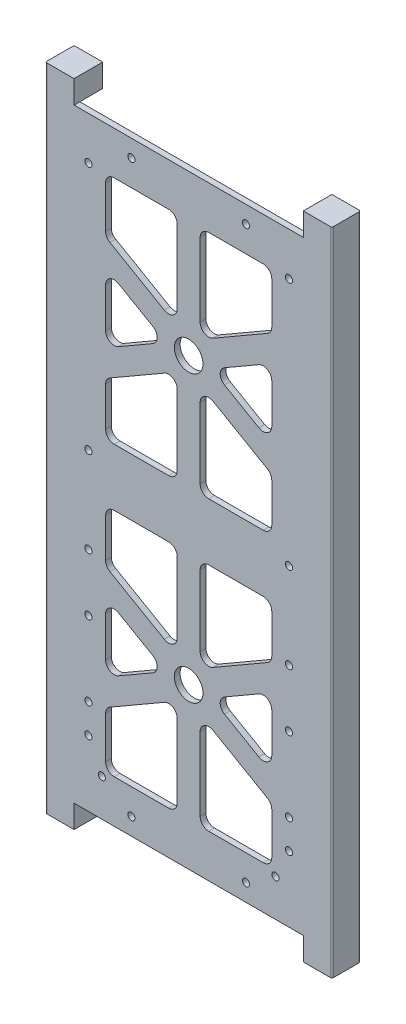
SolidWorks part; units mm, degrees
material "6061-T6 (SS)"
ref_plane "Front Plane" through (0, 0, 0) normal (0, 0, 1) x (1, 0, 0)
ref_plane "Top Plane" through (0, 0, 0) normal (0, 1, 0) x (1, 0, 0)
ref_plane "Right Plane" through (0, 0, 0) normal (1, 0, 0) x (0, 0, -1)
sketch "Sketch1" plane through (0, 0, 0) normal (0, 0, 1) x (1, 0, 0)
  line L1 (0, 0) -> (88, 0)
  line L2 (0, 0) -> (0, 211)
  line L3 (0, 211) -> (88, 211)
  line L4 (88, 0) -> (88, 211)
  dimension "D1" = 88
  dimension "D2" = 211
extrude "Boss-Extrude1" add sketch "Sketch1" along normal blind 2
sketch "Sketch2" plane through (0, 0, 2) normal (0, 0, 1) x (1, 0, 0)
  line L0 (0, 105.5) -> (88, 105.5) construction
  line L1 (0, 211) -> (0, 0) construction
  line L2 (88, 0) -> (88, 211) construction
  line L3 (44, 211) -> (44, 0) construction
  line L4 (88, 211) -> (0, 211) construction
  line L5 (0, 0) -> (88, 0) construction
  line L6 (0, 155.25) -> (88, 155.25) construction
  line L7 (0, 55.75) -> (88, 55.75) construction
  dimension "D1" = 55.75
  dimension "D2" = 55.75
sketch "Sketch3" plane through (0, 0, 2) normal (0, 0, 1) x (1, 0, 0)
  line L0 (0, 155.25) -> (88, 155.25) construction
  line L2 (0, 211) -> (0, 0) construction
  line L3 (15, 196) -> (73, 196)
  line L4 (15, 196) -> (15, 115.5)
  line L5 (15, 115.5) -> (73, 115.5)
  line L6 (73, 196) -> (73, 115.5)
  line L7 (88, 211) -> (0, 211) construction
  line L8 (88, 0) -> (88, 211) construction
  line L9 (0, 105.5) -> (88, 105.5) construction
  line L10 (40, 196) -> (40, 115.5)
  line L11 (48, 196) -> (48, 115.5)
  line L12 (44, 211) -> (44, 0) construction
  line L13 (73, 171.9932) -> (15, 138.5068) construction
  line L14 (15, 171.9932) -> (73, 138.5068) construction
  line L15 (73, 176.612) -> (15, 143.1256)
  line L16 (73, 167.3744) -> (15, 133.888)
  line L17 (15, 176.612) -> (73, 143.1256)
  line L18 (15, 167.3744) -> (73, 133.888)
  circle A0 centre (44, 155.25) radius 5
  dimension "D1" = 10
  dimension "D3" = 15
  dimension "D4" = 15
  dimension "D5" = 15
  dimension "D6" = 10
  dimension "D7" = 8
  dimension "D8" = 4
  dimension "D9" = 30
  dimension "D10" = 30
  dimension "D11" = 8
  dimension "D12" = 4
  dimension "D13" = 4
  dimension "D14" = 8
ref_plane "Plane1" through (0, 105.5, 0) normal (0, -1, 0) x (1, 0, 0)
extrude "Cut-Extrude2" cut sketch "Sketch3" against normal blind 2 contours L18 L11 L5 L6 | L10 L16 L4 L5 | L18 L4 L15 | L16 L17 L6 | L15 L6 L3 L11 | L4 L17 L10 L3
sketch "Sketch4" plane through (0, 0, 2) normal (0, 0, 1) x (1, 0, 0)
  line L0 (0, 155.25) -> (88, 155.25) construction
  circle A0 centre (44, 155.25) radius 5
  dimension "D1" = 10
extrude "Cut-Extrude3" cut sketch "Sketch4" against normal through all
mirror "Mirror2" about plane through (0, 105.5, 0) normal (0, -1, 0) of "Cut-Extrude3", "Cut-Extrude2"
fillet "Fillet2" radius 3 44 edges at (73, 67.8744, 1) (73, 43.6256, 1) (52, 55.75, 1) (40, 48.8218, 1) (40, 15, 1) (15, 15, 1) (15, 34.388, 1) (15, 143.1256, 1) (15, 167.3744, 1) (36, 155.25, 1) (15, 115.5, 1) (15, 133.888, 1) (40, 148.3218, 1) (40, 115.5, 1) (48, 196, 1) (73, 196, 1) (48, 162.1782, 1) (73, 115.5, 1) (48, 115.5, 1) (48, 148.3218, 1) (73, 133.888, 1) (15, 196, 1) (40, 196, 1) (40, 162.1782, 1) (15, 176.612, 1) (73, 167.3744, 1) (73, 143.1256, 1) (52, 155.25, 1) (48, 62.6782, 1) (48, 95.5, 1) (73, 95.5, 1) (73, 77.112, 1) (73, 34.388, 1) (73, 15, 1) (48, 15, 1) (48, 48.8218, 1) (40, 62.6782, 1) (15, 77.112, 1) (15, 95.5, 1) (40, 95.5, 1) (15, 43.6256, 1) (15, 67.8744, 1) (36, 55.75, 1) (73, 176.612, 1)
sketch "Sketch5" plane through (0, 0, 2) normal (0, 0, 1) x (1, 0, 0)
  line L0 (88, 0) -> (88, 211) construction
  line L1 (0, 211) -> (0, 0) construction
  line L4 (0, 5.5) -> (88, 5.5) construction
  line L5 (0, 0) -> (88, 0) construction
  line L6 (0, 205.5) -> (88, 205.5) construction
  circle A1 centre (64, 205.5) radius 1.5
  circle A3 centre (64, 5.5) radius 1.5
  circle A4 centre (24, 5.5) radius 1.5
  circle A5 centre (24, 205.5) radius 1.5
  dimension "D5" = 3
  dimension "D2" = 40
  dimension "D3" = 24
  dimension "D1" = 200
  dimension "D4" = 5.5
  dimension "D6" = 3
  dimension "D7" = 40
  dimension "D8" = 24
  dimension "D9" = 3
  dimension "D10" = 24
  dimension "D11" = 24
  dimension "D12" = 3
sketch "Sketch7" plane through (0, 0, 2) normal (0, 0, 1) x (1, 0, 0)
  line L0 (0, 105.5) -> (151.3859, 105.5) construction
  line L5 (0, 211) -> (0, 0) construction
  line L7 (44, 211) -> (44, 0) construction
  line L8 (88, 211) -> (0, 211) construction
  line L9 (0, 0) -> (88, 0) construction
  line L17 (94, 219) -> (84, 219)
  line L53 (88, 0) -> (88, 211)
  line L54 (84, 219) -> (84, 211)
  line L55 (84, 0) -> (88, 0)
  line L56 (94, 0) -> (94, 211)
  line L57 (94, -8) -> (94, 219)
  line L58 (88, 211) -> (0, 211) construction
  line L59 (84, 211) -> (88, 211)
  line L60 (84, -8) -> (84, 0)
  line L61 (94, -8) -> (84, -8)
  line L62 (-6, -8) -> (4, -8)
  line L63 (4, -8) -> (4, 0)
  line L64 (4, 0) -> (0, 0)
  line L65 (0, 0) -> (0, 211)
  line L66 (4, 211) -> (0, 211)
  line L67 (4, 219) -> (4, 211)
  line L68 (-6, 219) -> (4, 219)
  line L69 (-6, -8) -> (-6, 219)
  dimension "D1" = 6
extrude "Boss-Extrude2" add sketch "Sketch7" against normal blind 10
sketch "Sketch53" plane through (0, 0, -8) normal (0, 0, -1) x (-1, 0, 0)
  line L0 (-84, 0) -> (-84, 211)
  line L1 (-84, 211) -> (-90, 211)
  line L2 (-92, 209) -> (-92, 2)
  line L4 (-44, 0) -> (-44, 211)
  line L5 (-4, 0) -> (-84, 0) construction
  line L6 (-84, 211) -> (-4, 211) construction
  line L8 (-90, 0) -> (-84, 0)
  line L9 (4, 209) -> (4, 2)
  line L10 (-4, 211) -> (2, 211)
  line L11 (-4, 0) -> (-4, 211)
  line L12 (2, 0) -> (-4, 0)
  arc A0 (-92, 209) -> (-90, 211) centre (-90, 209) cw
  arc A1 (-90, 0) -> (-92, 2) centre (-90, 2) cw
  arc A2 (4, 209) -> (2, 211) centre (2, 209) ccw
  arc A3 (2, 0) -> (4, 2) centre (2, 2) ccw
  line M9 (-88, 0) -> (-88, 211)
  dimension "D1" = 2
  dimension "D2" = 2
extrude "Cut-Extrude5" cut sketch "Sketch53" against normal blind 8 contours A1 L8 L1 A0 L2 M9 | L12 A3 L9 A2 L10 L11
hole_wizard "M3x0.5 Tapped Hole1" positions "Sketch55" profile "Sketch56" tap size "M3x0.5" standard "ANSI Metric"
sketch "Sketch55" plane through (0, 0, 2) normal (0, 0, 1) x (1, 0, 0)
  line L0 (-6, 219) -> (-6, -8) construction
  line L1 (84, 211) -> (4, 211) construction
  line L3 (44, 211) -> (44, 0) construction
  line L4 (4, 0) -> (84, 0) construction
  line L5 (4, 0) -> (84, 0) construction
  line L6 (9, 33.2) -> (9, 211) construction
  point P4 (9, 109.2)
  point P6 (9, 79.2)
  point P8 (9, 59.2)
  point P10 (9, 33.2)
  point P25 (13.7, 13)
  point P40 (24, 205)
  point P42 (24, 6)
  point P44 (9, 23)
  point P47 (9, 196)
  dimension "D2" = 35
  dimension "D4" = 101.8
  dimension "D5" = 26
  dimension "D6" = 20
  dimension "D7" = 30
  dimension "D8" = 15
  dimension "D9" = 23
  dimension "D10" = 20
  dimension "D11" = 6
  dimension "D12" = 19.7
  dimension "D13" = 13
  dimension "D15" = 6
sketch "Sketch56" plane through (9, 109.2, 2) normal (1, 0, 0) x (0, -1, 0)
  line L0 (0, 0) -> (0, 10.7511)
  line L1 (0, 10.7511) -> (1.25, 10)
  line L2 (1.25, 10) -> (1.25, 0)
  line L5 (1.25, 0) -> (0, 0)
  line L10 (0, 10.7511) -> (-1.25, 10) construction
  line L11 (0, -6.35) -> (0, 107.95) construction
  dimension "Tap Drill Dia." = 2.5
  dimension "Tap Drill Depth" = 10
  dimension "Drill Angle" = 118
ref_plane "Plane2" through (44, 0, 0) normal (-1, 0, 0) x (0, 0, 1)
mirror "Mirror3" about plane through (44, 0, 0) normal (-1, 0, 0) of "M3x0.5 Tapped Hole1"
ref_plane "Plane3" through (44, 0, 0) normal (1, 0, 0) x (0, 0, -1)
sketch "Sketch58" plane through (0, 0, 0) normal (0, 0, -1) x (-1, 0, 0)
  line L0 (-13.7, 13) -> (6, 13) construction
  line L1 (6, 219) -> (6, -8) construction
  line L2 (-14.95, 13) -> (-12.45, 13) construction
  line L3 (-13.7, 11.75) -> (-13.7, 14.25) construction
  circle A0 centre (-0.7, 13) radius 1.665
  circle A1 centre (-13.7, 13) radius 1.25 construction
  point P9 (-13.7, 13)
  dimension "D1" = 3.33
  dimension "D2" = 13
extrude "Cut-Extrude9" cut sketch "Sketch58" against normal blind 1.8 contours A0
mirror "Mirror4" about plane through (44, 0, 0) normal (1, 0, 0) of "Cut-Extrude9"
sketch "Sketch59" plane through (0, -8, 0) normal (0, -1, 0) x (-1, 0, 0)
  line L0 (-94, 8) -> (-94, -2) construction
  line L1 (6, 8) -> (6, -2) construction
  line L2 (-84, 8) -> (-94, 8) construction
  circle A0 centre (-89, 2.4) radius 2
  circle A1 centre (1, 2.4) radius 2
  dimension "D1" = 4
  dimension "D2" = 5
  dimension "D3" = 5
  dimension "D4" = 5.6
extrude "Cut-Extrude10" cut sketch "Sketch59" against normal blind 10
fillet "Fillet3" radius 0.5 4 edges at (-6, 105.5, 2) (-6, 105.5, -8) (94, 105.5, -8) (94, 105.5, 2)
